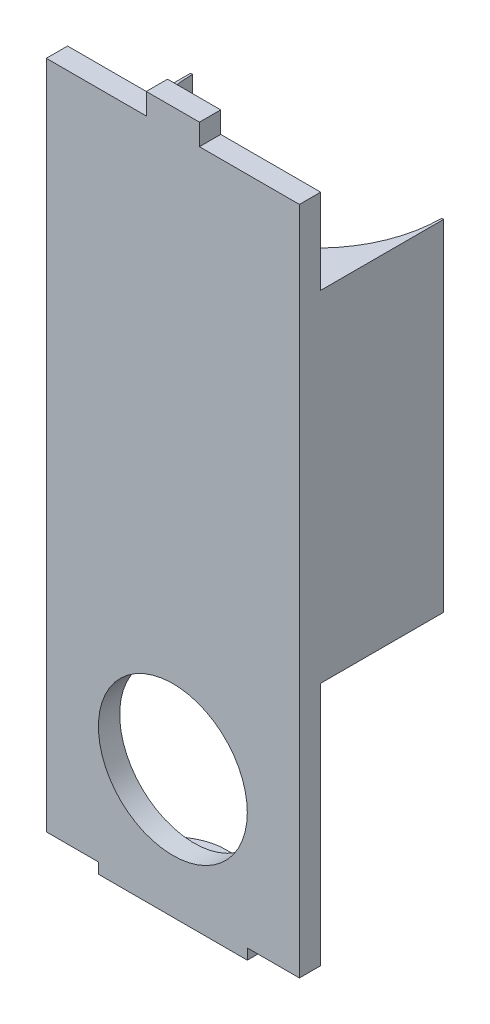
SolidWorks part; units mm, degrees
ref_plane "Front Plane" through (0, 0, 0) normal (0, 0, 1) x (1, 0, 0)
ref_plane "Top Plane" through (0, 0, 0) normal (0, 1, 0) x (1, 0, 0)
ref_plane "Right Plane" through (0, 0, 0) normal (1, 0, 0) x (0, 0, -1)
sketch "Sketch1" plane through (0, 0, 0) normal (0, 1, 0) x (1, 0, 0)
  line L0 (0, -0.4317) -> (0, 7.65)
  line L1 (-8.4894, 7.65) -> (8.4894, 7.65)
  line L2 (-14, -0.4317) -> (14, -0.4317)
  line L4 (-14, -0.4317) -> (-14, 14)
  line L5 (-14, 14) -> (14, 14)
  line L6 (14, 14) -> (14, -0.4317)
  line L7 (-14, -0.4317) -> (-14, -14)
  line L8 (-14, -14) -> (14, -14)
  line L9 (14, -14) -> (14, -0.4317)
  line L10 (-8.4894, -8.5135) -> (8.4894, -8.5135)
  line L11 (-14, -0.4317) -> (14, -0.4317)
  circle A0 centre (0, -0.4317) radius 11.7211
  point P7 (0, 7.65)
  point P12 (0, -0.4317)
extrude "Boss-Extrude1" add sketch "Sketch1" along normal blind 32 contours L10 A0 | A0 L2 L7 L8 L9 L11
sketch "Sketch2" plane through (-14, 0, 0) normal (-1, 0, 0) x (0, 0, 1)
  line L1 (0.4317, 32) -> (14, 32)
  line L2 (0.4317, 32) -> (0.4317, 0)
  line L3 (0.4317, 0) -> (14, 0)
  line L4 (14, 32) -> (14, 0)
extrude "Cut-Extrude1" cut sketch "Sketch2" against normal blind 2.1
mirror "Mirror1" about plane through (0, 0, 0) normal (1, 0, 0) of "Cut-Extrude1"
sketch "Sketch3" plane through (0, 0, 0) normal (0, -1, 0) x (1, 0, 0)
  line L0 (11.9, 0.4317) -> (11.9, 14) construction
  line L1 (-11.9, 14) -> (11.9, 14)
  line L2 (-11.9, 14) -> (-11.9, 12)
  line L3 (-11.9, 12) -> (11.9, 12)
  line L4 (11.9, 14) -> (11.9, 12)
  dimension "D1" = 2
extrude "Boss-Extrude2" add sketch "Sketch3" along normal blind 23 contours L2 L1 L4 L3
sketch "Sketch4" plane through (0, 32, 0) normal (0, 1, 0) x (1, 0, 0)
  line L0 (11.9, -14) -> (11.9, -0.4317) construction
  line L1 (-11.9, -14) -> (11.9, -14)
  line L2 (-11.9, -14) -> (-11.9, -12)
  line L3 (-11.9, -12) -> (11.9, -12)
  line L4 (11.9, -14) -> (11.9, -12)
  dimension "D1" = 2
extrude "Boss-Extrude3" add sketch "Sketch4" along normal blind 8
sketch "Sketch5" plane through (0, 0, 14) normal (0, 0, 1) x (1, 0, 0)
  line L0 (0, -7.4625) -> (0, 7.4625) construction
  circle A0 centre (0, -11.9701) radius 7
extrude "Cut-Extrude2" cut sketch "Sketch5" against normal up to next
sketch "Sketch6" plane through (0, 40, 0) normal (0, 1, 0) x (1, 0, 0)
  line L0 (0, -12) -> (0, -14)
  line L1 (11.9, -12) -> (-11.9, -12) construction
  line L2 (-11.9, -14) -> (11.9, -14) construction
  line L3 (11.9, -12) -> (-11.9, -12) construction
  line L4 (-2.5, -14) -> (2.5, -14)
  line L5 (-2.5, -14) -> (-2.5, -12)
  line L6 (-2.5, -12) -> (2.5, -12)
  line L7 (2.5, -14) -> (2.5, -12)
  line L8 (-2.5, -14) -> (2.5, -12) construction
  line L9 (-2.5, -12) -> (2.5, -14) construction
  point P6 (0, -13)
  line M7 (-11.9, -14) -> (11.9, -14)
  line M9 (11.9, -12) -> (-11.9, -12)
  dimension "D1" = 5
extrude "Boss-Extrude4" add sketch "Sketch6" along normal blind 2 contours L5 L0 M7 M9 | L7 L0 M7 M9
sketch "Sketch7" plane through (0, -23, 0) normal (0, -1, 0) x (1, 0, 0)
  line L0 (0, 14) -> (0, 12)
  line L1 (-11.9, 14) -> (11.9, 14) construction
  line L2 (-11.9, 12) -> (11.9, 12) construction
  line L4 (-7, 12) -> (7, 12)
  line L5 (-7, 12) -> (-7, 14)
  line L6 (-7, 14) -> (7, 14)
  line L7 (7, 12) -> (7, 14)
  line L8 (-7, 12) -> (7, 14) construction
  line L9 (-7, 14) -> (7, 12) construction
  point P6 (0, 13)
  line M5 (-11.9, 12) -> (11.9, 12)
  line M7 (11.9, 14) -> (-11.9, 14)
  dimension "D1" = 14
extrude "Boss-Extrude5" add sketch "Sketch7" along normal blind 1 contours L7 L0 M5 M7 | L5 L0 M5 M7
sketch "Sketch8" plane through (0, 0, 14) normal (0, 0, 1) x (1, 0, 0)
  line L1 (-7, -24) -> (7, -24)
  line L2 (-7, -24) -> (-7, -23)
  line L3 (-7, -23) -> (7, -23)
  line L4 (7, -24) -> (7, -23)
extrude "Boss-Extrude6" add sketch "Sketch8" against normal blind 5 from offset 2 offset against normal yes
sketch "Sketch9" plane through (0, -24, 0) normal (0, -1, 0) x (1, 0, 0)
  line L0 (0, 12) -> (0, 10.5)
  line L1 (-11.9, 12) -> (11.9, 12) construction
  line L2 (0, -7.4625) -> (0, 7.4625) construction
  line L3 (0, 10.5) -> (0, 9.5)
  circle A0 centre (0, 9.5) radius 1.5
extrude "Cut-Extrude3" cut sketch "Sketch9" against normal up to next
fillet "Fillet1" radius 5 2 edges at (-7, -23.5, 7) (7, -23.5, 7)
